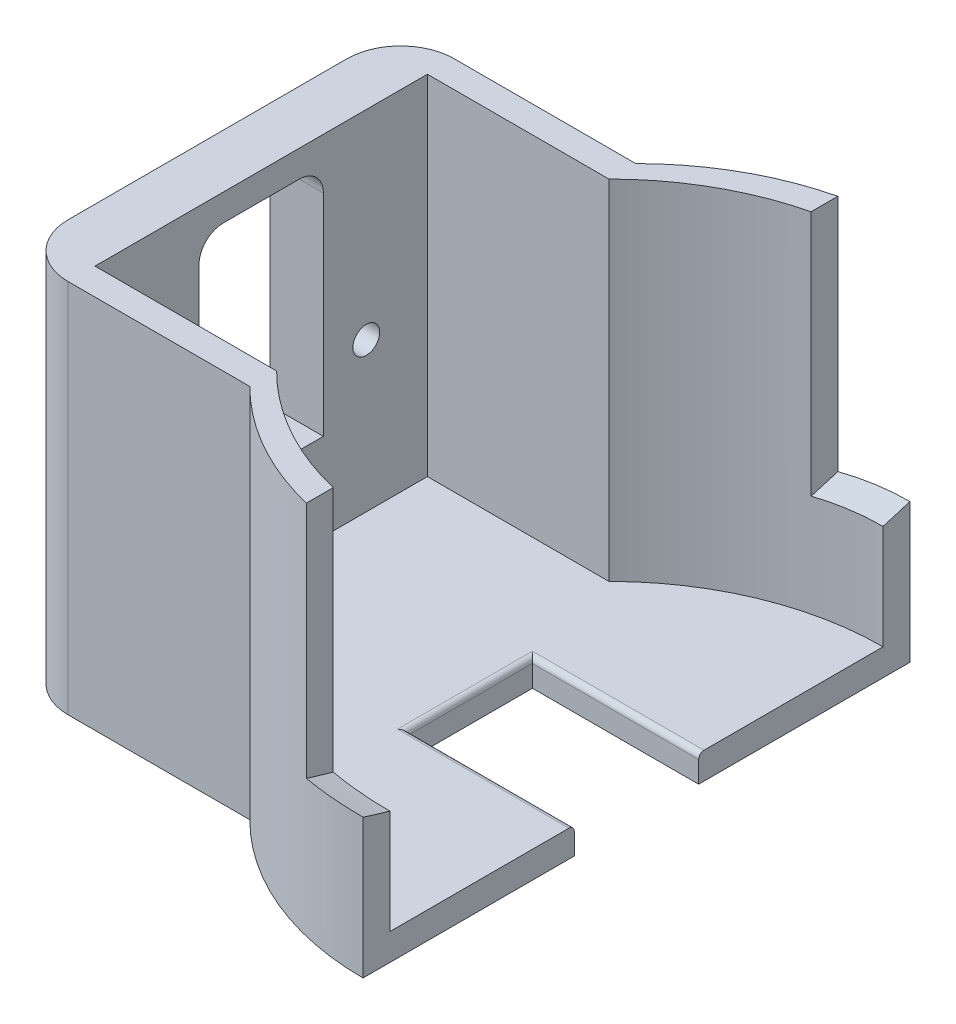
SolidWorks part; units mm, degrees
ref_plane "Plan de face" through (0, 0, 0) normal (0, 0, 1) x (1, 0, 0)
ref_plane "Plan de dessus" through (0, 0, 0) normal (0, 1, 0) x (1, 0, 0)
ref_plane "Plan de droite" through (0, 0, 0) normal (1, 0, 0) x (0, 0, -1)
sketch "Esquisse1" plane through (0, 0, 0) normal (0, 1, 0) x (1, 0, 0)
  line L0 (-50.0182, 0) -> (81.7007, 0) construction
  line L1 (0, 51) -> (0, 46)
  line L2 (-70, 31) -> (-36.1248, 31)
  line L3 (-70, 31) -> (-70, -31)
  line L4 (0, 46) -> (0, -46)
  line L5 (0, 68.3448) -> (0, -68.3448) construction
  line L6 (-36.1248, 36) -> (-80, 36)
  line L7 (-80, 36) -> (-80, -36)
  line L8 (-80, -36) -> (-36.1248, -36)
  line L9 (-70, -31) -> (-36.1248, -31)
  line L10 (0, -46) -> (0, -51)
  arc A0 (-36.1248, -36) -> (0, -51) centre (0, 0) ccw
  arc A1 (0, 51) -> (-36.1248, 36) centre (0, 0) ccw
  arc A2 (-36.1248, 31) -> (0, 46) centre (0, -5) cw
  arc A3 (-36.1248, -31) -> (0, -46) centre (0, 5) ccw
  point P14 (-50, 0)
  point P21 (-19.5576, 42.101)
  point P22 (-19.5576, 47.101)
  point P23 (-19.5576, -42.101)
  point P24 (-19.5576, -47.101)
  dimension "D6" = 102
  dimension "D1" = 5
  dimension "D2" = 72
  dimension "D3" = 80
  dimension "D4" = 10
  dimension "D5" = 5
  dimension "D7" = 5
  dimension "D8" = 5
extrude "Boss.-Extru.5" add sketch "Esquisse1" along normal mid plane 100 contours A3 L9 L3 L2 A2 L1 A1 L6 L7 L8 A0 L10
sketch "Esquisse5" plane through (-70, 0, 0) normal (1, 0, 0) x (0, 0, -1)
  line L1 (-11.6, -2) -> (11.6, -2)
  line L2 (-11.6, -2) -> (-11.6, -33.8)
  line L3 (-11.6, -33.8) -> (11.6, -33.8)
  line L4 (11.6, -2) -> (11.6, -33.8)
  line L5 (-11.6, -2) -> (-11.6, 5.5)
  line L6 (11.6, -2) -> (11.6, 5.5)
  line L7 (-7.1, 10) -> (7.1, 10)
  arc A0 (-11.6, 5.5) -> (-7.1, 10) centre (-7.1, 5.5) cw
  arc A1 (7.1, 10) -> (11.6, 5.5) centre (7.1, 5.5) cw
  circle A2 centre (0, 0) radius 2.15
  dimension "D3" = 4.3
  dimension "D6" = 4.5
  dimension "D7" = 4.5
  dimension "D1" = 2
  dimension "D2" = 11.6
  dimension "D4" = 43.8
  dimension "D5" = 23.2
  dimension "D8" = 12
extrude "Enlèv. mat.-Extru.1" cut sketch "Esquisse5" against normal blind 10 contours A2 L1 L6 A1 L7 A0 L5 | A2 L1 L2 L3 L4 | L1 A2 | L1 A2
sketch "Esquisse8" plane through (0, -50, 0) normal (0, 1, 0) x (1, 0, 0)
  line L0 (0, -51) -> (0, 51)
  line L1 (-36.1248, -36) -> (-80, -36)
  line L2 (-80, -36) -> (-80, 36)
  line L3 (-80, 36) -> (-36.1248, 36)
  arc A0 (0, 51) -> (-36.1248, 36) centre (0, 0) ccw construction
  arc A1 (0, -51) -> (-36.1248, -36) centre (0, 0) cw
  arc A2 (-36.1248, -36) -> (0, -51) centre (0, 0) ccw construction
  arc A3 (-36.1248, 36) -> (0, 51) centre (0, 0) cw
extrude "Boss.-Extru.6" add sketch "Esquisse8" against normal blind 5
sketch "Esquisse9" plane through (0, 0, 0) normal (1, 0, 0) x (0, 0, -1)
  line L0 (-51, 50) -> (-51, -55) construction
  line L1 (-51, 15) -> (51, 15)
  line L2 (-51, 15) -> (-51, 50)
  line L3 (-51, 50) -> (51, 50)
  line L4 (51, 15) -> (51, 50)
  line L5 (-7.1, 10) -> (7.1, 10) construction
  dimension "D1" = 5
extrude "Enlèv. mat.-Extru.2" cut sketch "Esquisse9" against normal through all
sketch "Esquisse10" plane through (0, 0, 0) normal (1, 0, 0) x (0, 0, -1)
  line L0 (85.2632, 65.694) -> (136.2871, 33.4867)
  line L1 (0, 23.2055) -> (0, -37) construction
  line L2 (-136.2871, 33.4867) -> (-85.2632, 65.694)
  line L3 (85.2632, 65.694) -> (136.2871, 33.4867) construction
  arc A0 (-85.2632, 65.694) -> (85.2632, 65.694) centre (0, 130) ccw
  arc A1 (-136.2871, 33.4867) -> (136.2871, 33.4867) centre (0, 130) ccw
  arc A3 (-73.5134, 52.5348) -> (49.5522, 35.3974) centre (0, 130) ccw
  point P0 (0, 23.2055)
  line M2 (-46, 15) -> (-51, 15)
  line M3 (-51, 15) -> (-51, -55)
  line M5 (51, -55) -> (51, 15)
  line M6 (51, 15) -> (46, 15)
  line M7 (46, 15) -> (46, -50)
  line M9 (-46, -50) -> (-46, 15)
  dimension "D3" = 37
  dimension "D7" = 167
  dimension "D10" = 11.7498
sketch "Esquisse11" plane through (-70, 0, 0) normal (1, 0, 0) x (0, 0, -1)
  line L0 (0, 0) -> (0, -23.2285) construction
  line L1 (-11.6, -2) -> (-11.6, -33.8) construction
  line L3 (31, -50) -> (-31, -50) construction
  line L5 (12.6, -50) -> (46, -50) construction
  circle A0 centre (-19.6, -22.214) radius 2.5
  circle A1 centre (19.6, -22.214) radius 2.5
  circle A2 centre (0, 126.5) radius 150
  point P6 (0, -23.5)
  dimension "D1" = 300
  dimension "D3" = 5
  dimension "D2" = 23.5
  dimension "D4" = 8
  dimension "D5" = 39.2
  dimension "D6" = 27.786
extrude "Enlèv. mat.-Extru.9" cut sketch "Esquisse11" against normal blind 5 contours A0 | A1
extrude "Enlèv. mat.-Extru.12" cut sketch "Esquisse10" against normal blind 12 contours L2 A1 L0 A0 M3 M2 M9 M7 M6 M5 | A1 M3 M9 M2 | A1 M7 M5 M6
fillet "Congé1" radius 10 2 edges at (-80, -20, 36) (-80, -20, -36)
sketch "Esquisse12" plane through (0, -55, 0) normal (0, -1, 0) x (-1, 0, 0)
  line L0 (5.4841, 0) -> (-5.4841, 0) construction
  line L8 (31, -11.6) -> (0, -11.6)
  line L9 (31, -11.6) -> (31, 11.6)
  line L10 (31, 11.6) -> (0, 11.6)
  line L11 (0, -11.6) -> (0, 11.6)
  line L12 (0, -51) -> (0, 51) construction
  dimension "D2" = 23.2
  dimension "D10" = 31
extrude "Enlèv. mat.-Extru.13" cut sketch "Esquisse12" against normal blind 10
fillet "Congé2" radius 1 3 edges at (-15.5, -50, -11.6) (-31, -50, 0) (-15.5, -50, 11.6)
